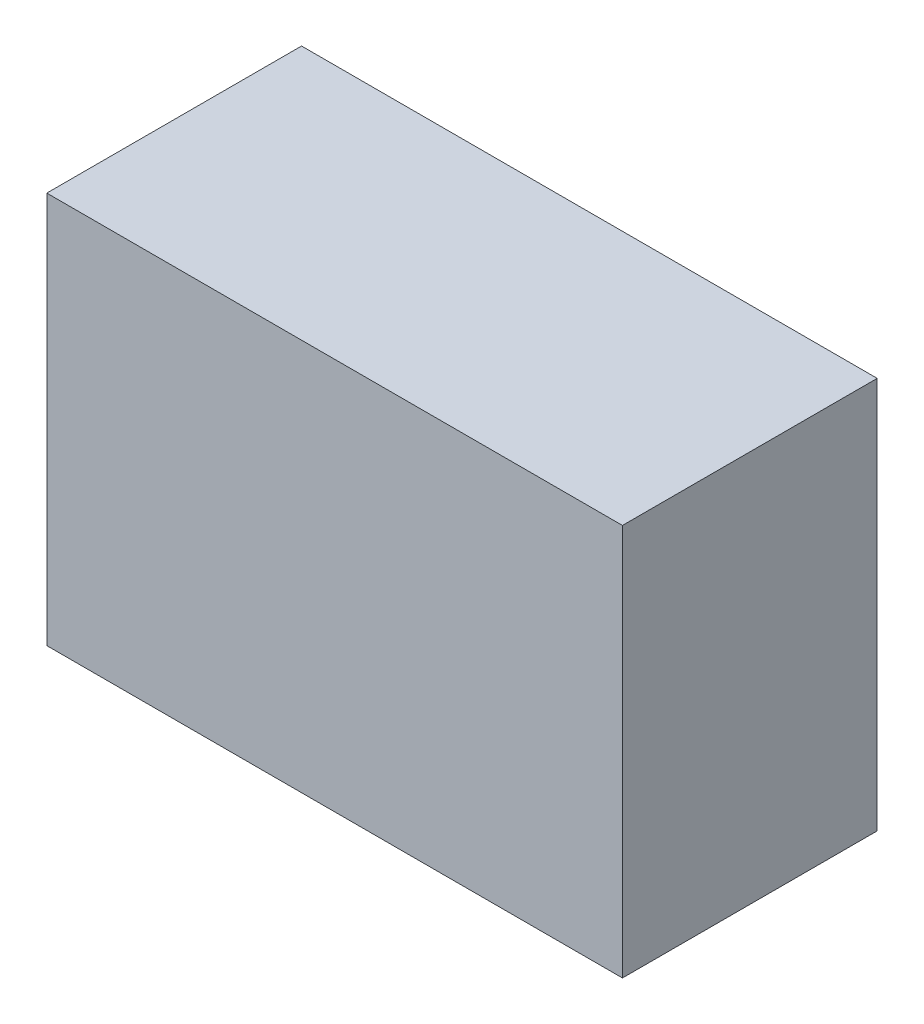
SolidWorks part; units mm, degrees
ref_plane "Front" through (0, 0, 0) normal (0, 0, 1) x (1, 0, 0)
ref_plane "Top" through (0, 0, 0) normal (0, 1, 0) x (1, 0, 0)
ref_plane "Right" through (0, 0, 0) normal (1, 0, 0) x (0, 0, -1)
sketch "Sketch2" plane through (0, 0, 0) normal (0, 1, 0) x (1, 0, 0)
  line L0 (-74.6125, 0) -> (74.6125, 0) construction
  line L1 (-74.6125, 33.02) -> (74.6125, 33.02)
  line L2 (-74.6125, 33.02) -> (-74.6125, -33.02)
  line L3 (-74.6125, -33.02) -> (74.6125, -33.02)
  line L4 (74.6125, 33.02) -> (74.6125, -33.02)
  dimension "D1" = 149.225
  dimension "D2" = 66.04
extrude "Extrude1" add sketch "Sketch2" along normal blind 101.6
